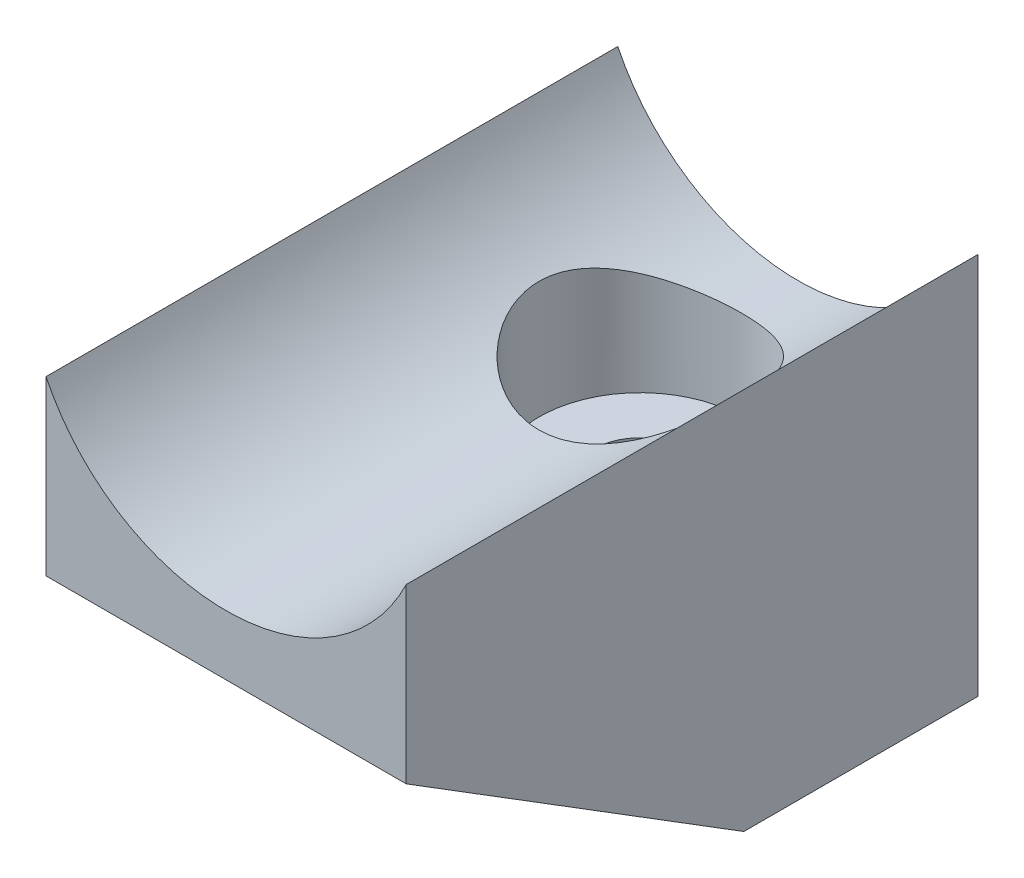
SolidWorks part; units mm, degrees
ref_plane "Front Plane" through (0, 0, 0) normal (0, 0, 1) x (1, 0, 0)
ref_plane "Top Plane" through (0, 0, 0) normal (0, 1, 0) x (1, 0, 0)
ref_plane "Right Plane" through (0, 0, 0) normal (1, 0, 0) x (0, 0, -1)
sketch "Sketch1" plane through (0, 0, 0) normal (0, 0, 1) x (1, 0, 0)
  line L0 (-180.1477, 0) -> (197.4813, 0) construction
  line L2 (0, -85.5209) -> (0, 332.6755) construction
sketch "Sketch2" plane through (0, 0, 0) normal (0, 0, 1) x (1, 0, 0)
  line L0 (0, 51) -> (0, 0)
  line L1 (0, 0) -> (48, 0)
  line L2 (-180.1477, 0) -> (197.4813, 0) construction
  line L3 (48, 0) -> (48, 51)
  arc A2 (0, 51) -> (48, 51) centre (24, 62.6701) ccw
  dimension "D1" = 26.6869
  dimension "D2" = 51
  dimension "D3" = 48
  dimension "D4" = 51
extrude "Boss-Extrude1" add sketch "Sketch2" along normal blind 76.2
ref_plane "Plane1" through (48, 0, 0) normal (-1, 0, 0) x (0, 0, 1)
sketch "Sketch3" plane through (48, 0, 0) normal (-1, 0, 0) x (0, 0, 1)
  line L5 (76.2, 28) -> (76.2, 0)
  line L6 (76.2, 0) -> (76.2, 51) construction
  line L7 (76.2, 0) -> (0, 0) construction
  line L8 (76.2, 0) -> (31.2, 0)
  line L9 (31.2, 0) -> (76.2, 28)
  dimension "D1" = 45
  dimension "D2" = 28
extrude "Cut-Extrude1" cut sketch "Sketch3" along normal blind 49.2
sketch "Sketch5" plane through (0, 0, 0) normal (0, -1, 0) x (1, 0, 0)
  line L0 (-180.1477, 0) -> (197.4813, 0) construction
  line L1 (0, 31.2) -> (0, 0) construction
  circle A0 centre (24, 21) radius 6.15
  dimension "D1" = 12.3
  dimension "D2" = 21
  dimension "D3" = 24
extrude "Cut-Extrude2" cut sketch "Sketch5" against normal blind 44
ref_plane "Plane3" through (0, 51, 0) normal (0, -1, 0) x (-1, 0, 0)
sketch "Sketch6" plane through (0, 51, 0) normal (0, -1, 0) x (-1, 0, 0)
  circle A0 centre (-24, -21) radius 13.5
  dimension "D1" = 27
extrude "Cut-Extrude3" cut sketch "Sketch6" along normal blind 27 contours A0
